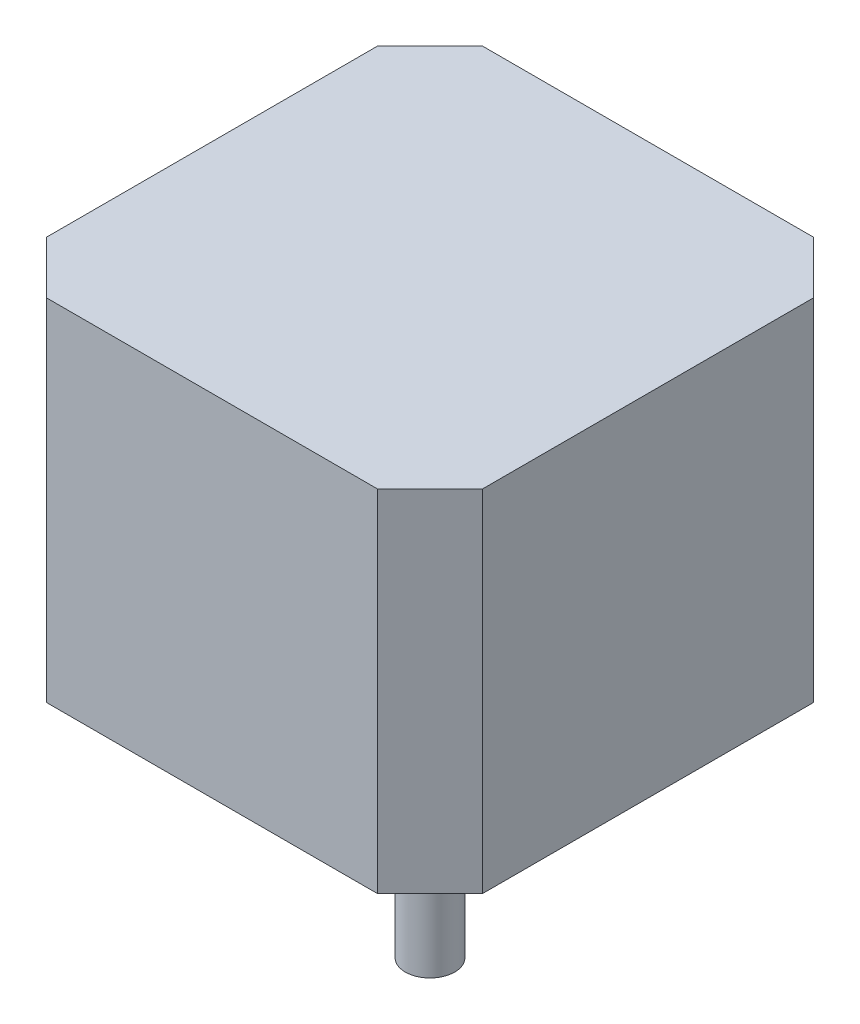
SolidWorks part; units mm, degrees
material "1060 Alloy"
ref_plane "Front Plane" through (0, 0, 0) normal (0, 0, 1) x (1, 0, 0)
ref_plane "Top Plane" through (0, 0, 0) normal (0, 1, 0) x (1, 0, 0)
ref_plane "Right Plane" through (0, 0, 0) normal (1, 0, 0) x (0, 0, -1)
sketch "Sketch1" plane through (0, 0, 0) normal (0, 1, 0) x (1, 0, 0)
  line L11 (-21.15, -16.07) -> (-21.15, 16.07)
  line L12 (-16.07, 21.15) -> (16.07, 21.15)
  line L13 (21.15, 16.07) -> (21.15, -16.07)
  line L14 (16.07, -21.15) -> (-16.07, -21.15)
  line L15 (-21.15, 16.07) -> (-16.07, 21.15)
  line L16 (16.07, 21.15) -> (21.15, 16.07)
  line L17 (-16.07, -21.15) -> (-21.15, -16.07)
  line L18 (21.15, -16.07) -> (16.07, -21.15)
  line L19 (-21.15, 0) -> (21.15, 0) construction
  point P0 (-21.15, -21.15)
  point P1 (-21.15, 21.15)
  point P2 (21.15, 21.15)
  point P3 (21.15, -21.15)
  point P15 (0, 0)
  dimension "D2" = 42.3
  dimension "D3" = 42.3
extrude "Boss-Extrude1" add sketch "Sketch1" along normal blind 34
hole_wizard "M3x0.5 Tapped Hole1" positions "Sketch2" profile "Sketch3" tap size "M3x0.5" standard "ANSI Metric"
sketch "Sketch2" plane through (0, 0, 0) normal (0, -1, 0) x (-1, 0, 0)
  line L0 (-15.5, 15.5) -> (-15.5, -15.5) construction
  line L1 (-15.5, -15.5) -> (15.5, -15.5) construction
  line L2 (15.5, -15.5) -> (15.5, 15.5) construction
  line L3 (15.5, 15.5) -> (-15.5, 15.5) construction
  line L5 (-15.5, -15.5) -> (15.5, 15.5) construction
  point P0 (-15.5, 15.5)
  point P2 (15.5, 15.5)
  point P4 (15.5, -15.5)
  point P6 (-15.5, -15.5)
  dimension "D1" = 31
sketch "Sketch3" plane through (15.5, 0, -15.5) normal (1, 0, 0) x (0, 0, -1)
  line L0 (0, 0) -> (0, 5.2511)
  line L1 (0, 5.2511) -> (1.25, 4.5)
  line L2 (1.25, 4.5) -> (1.25, 0)
  line L5 (1.25, 0) -> (0, 0)
  line L10 (0, 5.2511) -> (-1.25, 4.5) construction
  line L11 (0, -6.35) -> (0, 107.95) construction
  dimension "Tap Drill Dia." = 2.5
  dimension "Tap Drill Depth" = 4.5
  dimension "Drill Angle" = 118
cosmetic thread "Hole Thread1" parameters "D1"=3.5, "D2"=3
cosmetic thread "Hole Thread2" parameters "D1"=3.5, "D2"=3
cosmetic thread "Hole Thread3" parameters "D1"=3.5, "D2"=3
cosmetic thread "Hole Thread4" parameters "D1"=3.5, "D2"=3
sketch "Sketch4" plane through (0, 0, 0) normal (0, -1, 0) x (-1, 0, 0)
  line L0 (-21.15, 0) -> (21.15, 0) construction
  line L1 (-21.15, -16.07) -> (-21.15, 16.07) construction
  line L2 (21.15, 16.07) -> (21.15, -16.07) construction
  line L3 (0, 21.15) -> (0, -21.15) construction
  line L4 (-16.07, 21.15) -> (16.07, 21.15) construction
  line L5 (16.07, -21.15) -> (-16.07, -21.15) construction
  circle A0 centre (0, 0) radius 11
  dimension "D1" = 22
extrude "Boss-Extrude2" add sketch "Sketch4" along normal blind 2
sketch "Sketch5" plane through (0, -2, 0) normal (0, -1, 0) x (1, 0, 0)
  line L0 (1.524, -1.8489) -> (-1.524, -1.8489)
  arc A0 (1.524, -1.8489) -> (-1.524, -1.8489) centre (0, 0) ccw
  dimension "D1" = 4.792
  dimension "D2" = 3.048
extrude "Boss-Extrude3" add sketch "Sketch5" along normal blind 22
sketch "Sketch6" plane through (-21.15, 0, 0) normal (-1, 0, 0) x (0, 0, 1)
  line L0 (-1.905, 34) -> (-1.905, 32.73) construction
  line L1 (-16.07, 34) -> (16.07, 34) construction
  line L2 (-1.905, 32.73) -> (1.905, 32.73) construction
  line L3 (1.905, 32.73) -> (1.905, 34) construction
  line L4 (-1.905, 34) -> (1.905, 34) construction
  circle A0 centre (-1.905, 32.73) radius 0.635
  circle A1 centre (-0.635, 32.73) radius 0.635
  circle A2 centre (0.635, 32.73) radius 0.635
  circle A3 centre (1.905, 32.73) radius 0.635
  point P9 (0, 34)
  point P13 (0, 34)
  dimension "D2" = 1.27
  dimension "D1" = 1.27
